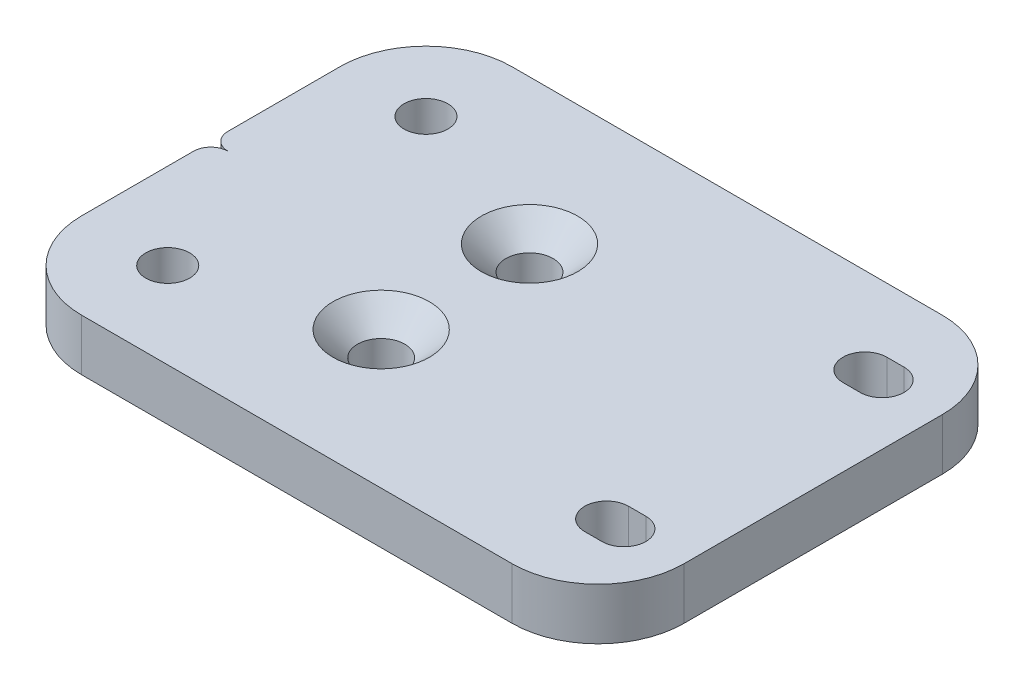
SolidWorks part; units mm, degrees
material "Клен"
ref_plane "Спереди" through (0, 0, 0) normal (0, 0, 1) x (1, 0, 0)
ref_plane "Сверху" through (0, 0, 0) normal (0, 1, 0) x (1, 0, 0)
ref_plane "Справа" through (0, 0, 0) normal (1, 0, 0) x (0, 0, -1)
sketch "Эскиз1" plane through (0, 0, 0) normal (0, 1, 0) x (1, 0, 0)
  line L0 (-41.181, -0.0464) -> (44.1026, -0.0464) construction
  line L10 (-25, -25) -> (25, -25)
  line L11 (-35, -15) -> (-35, 15)
  line L12 (-25, 25) -> (25, 25)
  line L13 (35, -15) -> (35, 15)
  line L14 (-35, -25) -> (35, 25) construction
  line L15 (-35, 25) -> (35, -25) construction
  arc A4 (25, 25) -> (35, 15) centre (25, 15) cw
  arc A5 (25, -25) -> (35, -15) centre (25, -15) ccw
  arc A6 (-25, -25) -> (-35, -15) centre (-25, -15) cw
  arc A7 (-35, 15) -> (-25, 25) centre (-25, 15) cw
  point P0 (0, 0)
  dimension "D1" = 10
  dimension "D2" = 50
  dimension "D3" = 70
extrude "Бобышка-Вытянуть1" add sketch "Эскиз1" along normal blind 6
sketch "Эскиз2" plane through (0, 0, 0) normal (0, -1, 0) x (1, 0, 0)
  line L0 (0, -37.0349) -> (0, 29.2907) construction
  line L1 (28, -15) -> (26, -15) construction
  line L2 (28, -17.55) -> (26, -17.55)
  line L3 (28, -12.45) -> (26, -12.45)
  line L6 (-46.1924, 0) -> (55.6646, 0) construction
  line L7 (28, 15) -> (26, 15) construction
  line L8 (28, 17.55) -> (26, 17.55)
  line L9 (28, 12.45) -> (26, 12.45)
  line L10 (-35, -15) -> (-35, 15) construction
  line L11 (25, -25) -> (-25, -25) construction
  circle A0 centre (-25, -15) radius 2.55
  arc A1 (28, -17.55) -> (28, -12.45) centre (28, -15) ccw
  arc A2 (26, -12.45) -> (26, -17.55) centre (26, -15) ccw
  arc A3 (28, 17.55) -> (28, 12.45) centre (28, 15) cw
  arc A4 (26, 12.45) -> (26, 17.55) centre (26, 15) cw
  circle A5 centre (-25, 15) radius 2.55
  point P7 (27, -15)
  point P12 (27, -17.55)
  point P21 (27, 15)
  dimension "D1" = 5.1
  dimension "D2" = 5.1
  dimension "D3" = 2
  dimension "D4" = 53
  dimension "D5" = 10
  dimension "D6" = 10
extrude "Вырез-Вытянуть1" cut sketch "Эскиз2" against normal through all
sketch "Эскиз3" plane through (0, 0, 0) normal (0, -1, 0) x (1, 0, 0)
  line L0 (-33, 0) -> (27.7687, 0) construction
  line L1 (-35, -15) -> (-35, 15) construction
  line L2 (-35, -2) -> (-35, 2)
  arc A0 (-33, 0) -> (-35, -2) centre (-33, -2) ccw
  arc A1 (-33, 0) -> (-35, 2) centre (-33, 2) cw
  point P3 (-35, -2)
  point P4 (-33, 0)
  point P7 (-35, 2)
  dimension "D2" = 2
  dimension "D1" = 2
extrude "Вырез-Вытянуть2" cut sketch "Эскиз3" against normal through all
hole_wizard "Зенковка для  винта с потайной головкой с внутренним шестигранником M52" positions "Эскиз6" profile "Эскиз7" countersink size "M5" standard "Ansi Metric" end condition through all
sketch "Эскиз6" plane through (0, 6, 0) normal (0, 1, 0) x (1, 0, 0)
  point P0 (-6.1594, -9.0403)
  point P2 (-6.1594, 8.1926)
sketch "Эскиз7" plane through (-6.1594, 6, 9.0403) normal (1, 0, 0) x (0, 0, 1)
  line L0 (0, 0) -> (0, 6)
  line L1 (0, 6) -> (2.75, 6)
  line L2 (2.75, 6) -> (2.75, 2.85)
  line L3 (2.75, 2.85) -> (5.6, 0)
  line L5 (5.6, 0) -> (0, 0)
  line L6 (-2.75, 2.85) -> (-5.6, 0) construction
  line L11 (0, -6.35) -> (0, 107.95) construction
  dimension "Диаметр сквозного отверстия" = 5.5
  dimension "Глубина сквозного отверстия" = 6
  dimension "Диаметр передней зенковки" = 11.2
  dimension "Угол передней зенковки" = 90
equation "\"D2@Эскиз2\"= \"D1@Эскиз2\""
